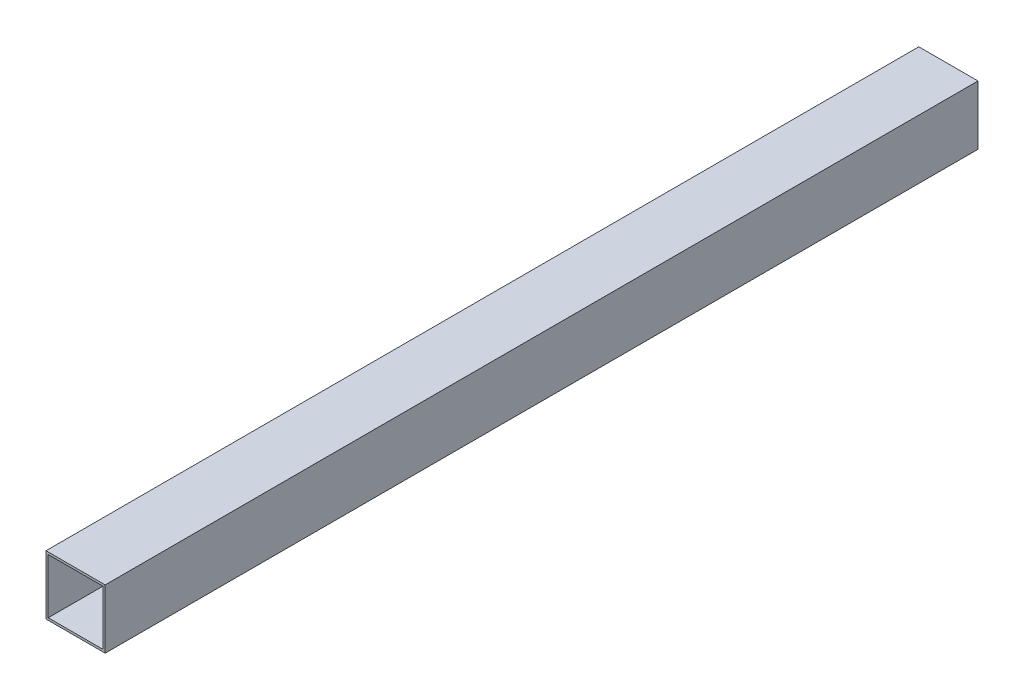
SolidWorks part; units mm, degrees
material "AISI 1020"
ref_plane "Plano frontal" through (0, 0, 0) normal (0, 0, 1) x (1, 0, 0)
ref_plane "Plano superior" through (0, 0, 0) normal (0, 1, 0) x (1, 0, 0)
ref_plane "Plano direito" through (0, 0, 0) normal (1, 0, 0) x (0, 0, -1)
sketch "Esboço1" plane through (0, 0, 0) normal (0, 0, 1) x (1, 0, 0)
  line L1 (-20, -20) -> (20, -20)
  line L2 (-20, -20) -> (-20, 20)
  line L3 (-20, 20) -> (20, 20)
  line L4 (20, -20) -> (20, 20)
  line L5 (-20, -20) -> (20, 20) construction
  line L6 (-20, 20) -> (20, -20) construction
  point P0 (0, 0)
  dimension "D1" = 40
  dimension "D2" = 40
extrude "Ressalto-extrusão1" add sketch "Esboço1" along normal blind 590
sketch "Esboço2" plane through (0, 0, 590) normal (0, 0, 1) x (1, 0, 0)
  line L1 (-18.5, -18.5) -> (18.5, -18.5)
  line L2 (-18.5, -18.5) -> (-18.5, 18.5)
  line L3 (-18.5, 18.5) -> (18.5, 18.5)
  line L4 (18.5, -18.5) -> (18.5, 18.5)
  line L5 (-18.5, -18.5) -> (18.5, 18.5) construction
  line L6 (-18.5, 18.5) -> (18.5, -18.5) construction
  point P0 (0, 0)
  dimension "D1" = 37
  dimension "D2" = 37
extrude "Corte-extrusão1" cut sketch "Esboço2" against normal through all
